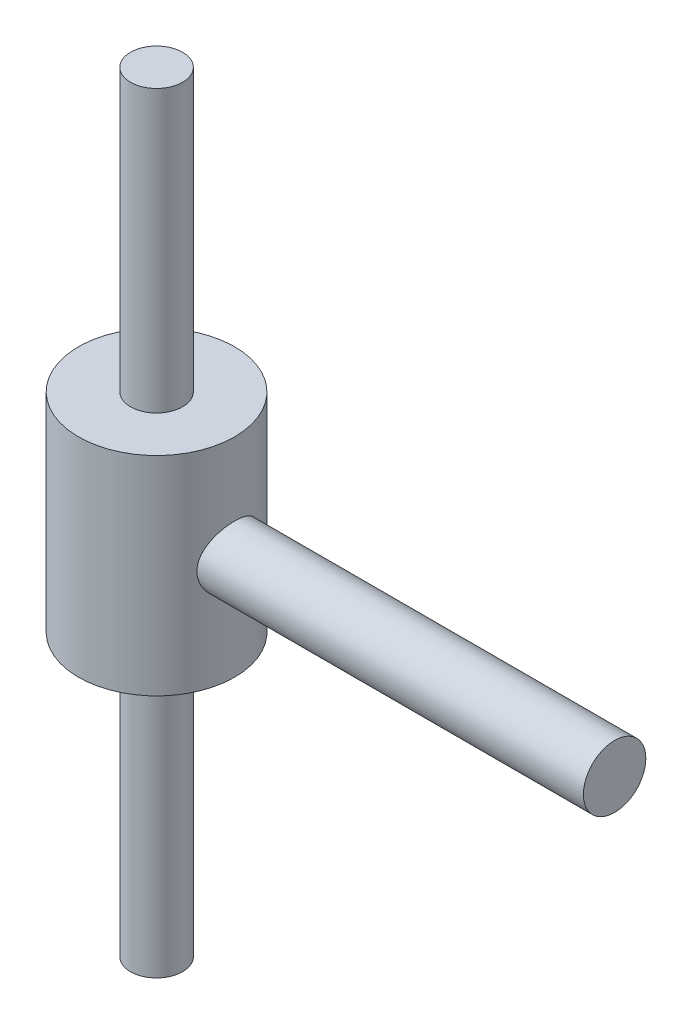
SolidWorks part; units mm, degrees
ref_plane "Front Plane" through (0, 0, 0) normal (0, 0, 1) x (1, 0, 0)
ref_plane "Top Plane" through (0, 0, 0) normal (0, 1, 0) x (1, 0, 0)
ref_plane "Right Plane" through (0, 0, 0) normal (1, 0, 0) x (0, 0, -1)
sketch "Sketch1" plane through (0, 0, 0) normal (0, 0, 1) x (1, 0, 0)
  line L0 (0, 74) -> (0, -74) construction
  line L5 (0, 20) -> (0, -20)
  point P0 (0, 0)
  point P3 (0, 0)
  point P6 (0, 0)
  dimension "D1" = 148
  dimension "D2" = 40
sweep "Sweep2" add path "Sketch1" circular profile diameter 30 parameters "D3"=30
sketch "Sketch30" plane through (0, 0, 0) normal (0, 0, 1) x (1, 0, 0)
  line L0 (0, 0) -> (88, 0)
  dimension "D1" = 88
sweep "Sweep3" add path "Sketch30" circular profile diameter 12 parameters "D3"=12
sketch "Sketch39" plane through (0, 0, 0) normal (0, 0, 1) x (1, 0, 0)
  line L0 (0, -20) -> (0, -74)
  line L1 (-15, -20) -> (15, -20) construction
  dimension "D1" = 74
sweep "Sweep4" add path "Sketch39" circular profile diameter 10 parameters "D3"=10
sketch "Sketch45" plane through (0, 0, 0) normal (0, 0, 1) x (1, 0, 0)
  line L0 (0, 20) -> (0, 74)
  line L1 (15, 20) -> (-15, 20) construction
  dimension "D1" = 74
sweep "Sweep5" add path "Sketch45" circular profile diameter 10 parameters "D3"=10
